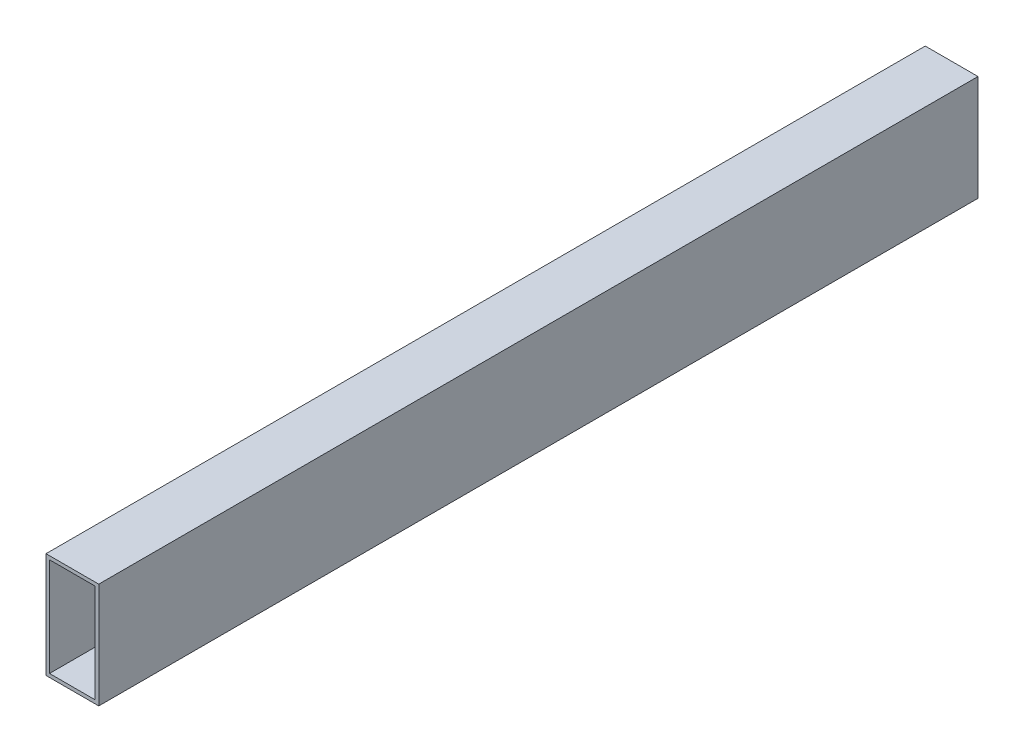
SolidWorks part; units mm, degrees
ref_plane "Front Plane" through (0, 0, 0) normal (0, 0, 1) x (1, 0, 0)
ref_plane "Top Plane" through (0, 0, 0) normal (0, 1, 0) x (1, 0, 0)
ref_plane "Right Plane" through (0, 0, 0) normal (1, 0, 0) x (0, 0, -1)
curve "Curve1"
  spline degree 1 poles (0, 0, -500) (0, 0, 500) knots 0 0 1 1
sketch "Sketch1" plane through (0, 0, 0) normal (0, 0, 1) x (1, 0, 0)
  line L0 (0, 35.3535) -> (0, -33.8384) construction
  line L1 (-30, 60) -> (30, 60)
  line L2 (-30, 60) -> (-30, -60)
  line L3 (-30, -60) -> (30, -60)
  line L4 (30, 60) -> (30, -60)
  line L5 (-26, 56) -> (26, 56)
  line L6 (-26, 56) -> (-26, -56)
  line L7 (-26, -56) -> (26, -56)
  line L8 (26, 56) -> (26, -56)
  line L9 (-39.3939, 0) -> (41.5152, 0) construction
  dimension "D1" = 60
  dimension "D2" = 52
  dimension "D3" = 120
  dimension "D4" = 112
sweep "Sweep1" add profiles "Sketch1" path "Curve1"
